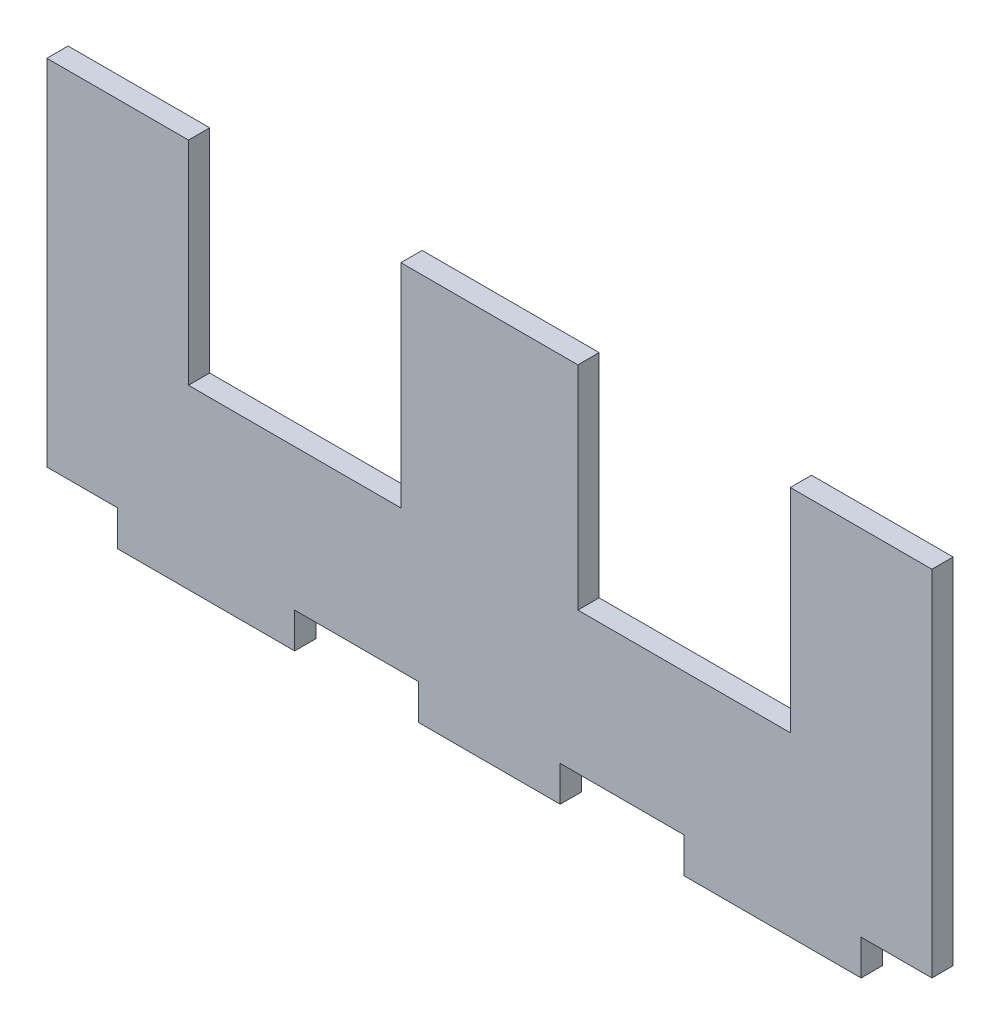
SolidWorks part; units mm, degrees
ref_plane "Plano frontal" through (0, 0, 0) normal (0, 0, 1) x (1, 0, 0)
ref_plane "Plano superior" through (0, 0, 0) normal (0, 1, 0) x (1, 0, 0)
ref_plane "Plano direito" through (0, 0, 0) normal (1, 0, 0) x (0, 0, -1)
sketch "Esboço1" plane through (0, 0, 0) normal (0, 0, 1) x (1, 0, 0)
  line L0 (-38.4908, -22.8963) -> (-20.9908, -22.8963)
  line L1 (-73.4908, 27.1037) -> (51.5092, 27.1037)
  line L2 (-73.4908, 27.1037) -> (-73.4908, -22.8963)
  line L3 (-73.4908, -22.8963) -> (-63.4908, -22.8963)
  line L4 (51.5092, 27.1037) -> (51.5092, -22.8963)
  line L5 (-0.9908, -22.8963) -> (16.5092, -22.8963)
  line L6 (-63.4908, -22.8963) -> (-63.4908, -27.8963)
  line L7 (-63.4908, -27.8963) -> (-38.4908, -27.8963)
  line L8 (-38.4908, -22.8963) -> (-38.4908, -27.8963)
  line L9 (41.5092, -22.8963) -> (51.5092, -22.8963)
  line L10 (-20.9908, -22.8963) -> (-20.9908, -27.8963)
  line L11 (-20.9908, -27.8963) -> (-0.9908, -27.8963)
  line L12 (-0.9908, -22.8963) -> (-0.9908, -27.8963)
  line L14 (16.5092, -22.8963) -> (16.5092, -27.8963)
  line L15 (16.5092, -27.8963) -> (41.5092, -27.8963)
  line L16 (41.5092, -22.8963) -> (41.5092, -27.8963)
  dimension "D1" = 125
  dimension "D2" = 50
  dimension "D3" = 10
  dimension "D4" = 25
  dimension "D5" = 5
  dimension "D6" = 5
  dimension "D7" = 5
  dimension "D8" = 17.5
  dimension "D9" = 20
  dimension "D10" = 25
  dimension "D11" = 10
extrude "Ressalto-extrusão1" add sketch "Esboço1" along normal blind 3
sketch "Esboço2" plane through (0, 0, 0) normal (0, 0, -1) x (-1, 0, 0)
  line L0 (-51.5092, 27.1037) -> (73.4908, 27.1037) construction
  line L1 (-31.5092, 27.1037) -> (-1.5092, 27.1037)
  line L2 (-31.5092, 27.1037) -> (-31.5092, -2.8963)
  line L3 (-31.5092, -2.8963) -> (-1.5092, -2.8963)
  line L4 (-1.5092, 27.1037) -> (-1.5092, -2.8963)
  line L5 (-51.5092, -22.8963) -> (-51.5092, 27.1037) construction
  line L6 (53.4908, -2.8963) -> (23.4908, -2.8963)
  line L7 (53.4908, -2.8963) -> (53.4908, 27.1037)
  line L8 (53.4908, 27.1037) -> (23.4908, 27.1037)
  line L9 (23.4908, -2.8963) -> (23.4908, 27.1037)
  line L10 (73.4908, 27.1037) -> (73.4908, -22.8963) construction
  dimension "D1" = 30
  dimension "D2" = 20
  dimension "D3" = 30
  dimension "D4" = 30
  dimension "D5" = 30
  dimension "D6" = 20
extrude "Corte-extrusão1" cut sketch "Esboço2" against normal through all
